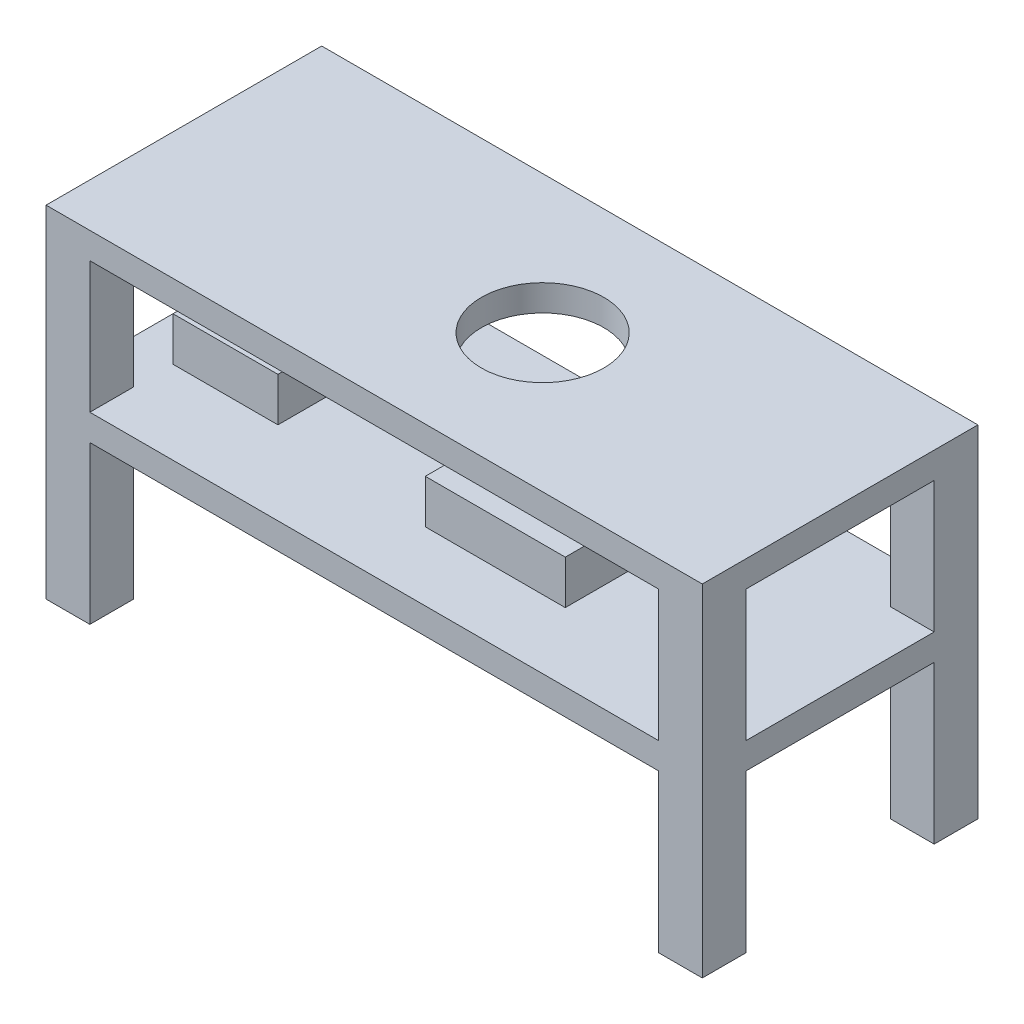
SolidWorks part; units mm, degrees
ref_plane "Front Plane" through (0, 0, 0) normal (0, 0, 1) x (1, 0, 0)
ref_plane "Top Plane" through (0, 0, 0) normal (0, 1, 0) x (1, 0, 0)
ref_plane "Right Plane" through (0, 0, 0) normal (1, 0, 0) x (0, 0, -1)
sketch "Sketch1" plane through (0, 0, 0) normal (0, 1, 0) x (1, 0, 0)
  line L1 (952.5, -400.05) -> (-952.5, -400.05)
  line L2 (952.5, -400.05) -> (952.5, 400.05)
  line L3 (952.5, 400.05) -> (-952.5, 400.05)
  line L4 (-952.5, -400.05) -> (-952.5, 400.05)
  line L5 (0, 400.05) -> (0, -400.05) construction
  line L6 (952.5, 0) -> (-952.5, 0) construction
  point P0 (0, 0)
  dimension "D1" = 1905
  dimension "D2" = 800.1
extrude "Boss-Extrude1" add sketch "Sketch1" along normal blind 76.2
sketch "Sketch2" plane through (0, 76.2, 0) normal (0, -1, 0) x (1, 0, 0)
  line L1 (952.5, -400.05) -> (-952.5, -400.05)
  line L2 (952.5, -400.05) -> (952.5, 400.05)
  line L3 (952.5, 400.05) -> (-952.5, 400.05)
  line L4 (-952.5, -400.05) -> (-952.5, 400.05)
  line L5 (0, 400.05) -> (0, -400.05) construction
  line L6 (952.5, 0) -> (-952.5, 0) construction
  point P0 (0, 0)
extrude "Boss-Extrude2" add sketch "Sketch2" along normal blind 76.2 from offset 457.2 separate body
sketch "Sketch3" plane through (0, 76.2, 0) normal (0, 1, 0) x (1, 0, 0)
  line L1 (-952.5, -400.05) -> (-825.5, -400.05)
  line L2 (-952.5, -400.05) -> (-952.5, -273.05)
  line L3 (-952.5, -273.05) -> (-825.5, -273.05)
  line L4 (-825.5, -400.05) -> (-825.5, -273.05)
  line L9 (952.5, 400.05) -> (825.5, 400.05)
  line L10 (952.5, 400.05) -> (952.5, 273.05)
  line L11 (952.5, 273.05) -> (825.5, 273.05)
  line L12 (825.5, 400.05) -> (825.5, 273.05)
  line L25 (-952.5, 400.05) -> (-825.5, 400.05)
  line L26 (-952.5, 400.05) -> (-952.5, 273.05)
  line L27 (-952.5, 273.05) -> (-825.5, 273.05)
  line L28 (-825.5, 400.05) -> (-825.5, 273.05)
  line L29 (952.5, -400.05) -> (825.5, -400.05)
  line L30 (952.5, -400.05) -> (952.5, -273.05)
  line L31 (952.5, -273.05) -> (825.5, -273.05)
  line L32 (825.5, -400.05) -> (825.5, -273.05)
  dimension "D1" = 127
  dimension "D2" = 127
  dimension "D3" = 127
  dimension "D4" = 127
extrude "Boss-Extrude3" add sketch "Sketch3" against normal blind 990.6
sketch "Sketch4" plane through (0, 76.2, 0) normal (0, 1, 0) x (1, 0, 0)
  line L0 (952.5, -400.05) -> (952.5, 400.05) construction
  circle A0 centre (88.9, 0) radius 177.8
  dimension "D1" = 355.6
  dimension "D2" = 863.6
extrude "Cut-Extrude1" cut sketch "Sketch4" against normal blind 76.2
sketch "Sketch5" plane through (0, -381, 0) normal (0, 1, 0) x (1, 0, 0)
  line L1 (-50.5146, -201.2242) -> (355.8854, -201.2242)
  line L2 (-50.5146, -201.2242) -> (-50.5146, 205.1758)
  line L3 (-50.5146, 205.1758) -> (355.8854, 205.1758)
  line L4 (355.8854, -201.2242) -> (355.8854, 205.1758)
  dimension "D1" = 406.4
  dimension "D2" = 406.4
extrude "Control Box" add sketch "Sketch5" along normal blind 127
sketch "Sketch6" plane through (0, -381, 0) normal (0, 1, 0) x (1, 0, 0)
  line L0 (-952.5, 400.05) -> (-952.5, -400.05) construction
  line L1 (-825.5, 146.05) -> (-520.7, 146.05)
  line L2 (-825.5, 146.05) -> (-825.5, -158.75)
  line L3 (-825.5, -158.75) -> (-520.7, -158.75)
  line L4 (-520.7, 146.05) -> (-520.7, -158.75)
  line L5 (952.5, 400.05) -> (-952.5, 400.05) construction
  dimension "D1" = 304.8
  dimension "D2" = 304.8
  dimension "D3" = 127
  dimension "D4" = 254
extrude "Spectrometer" add sketch "Sketch6" along normal blind 127
